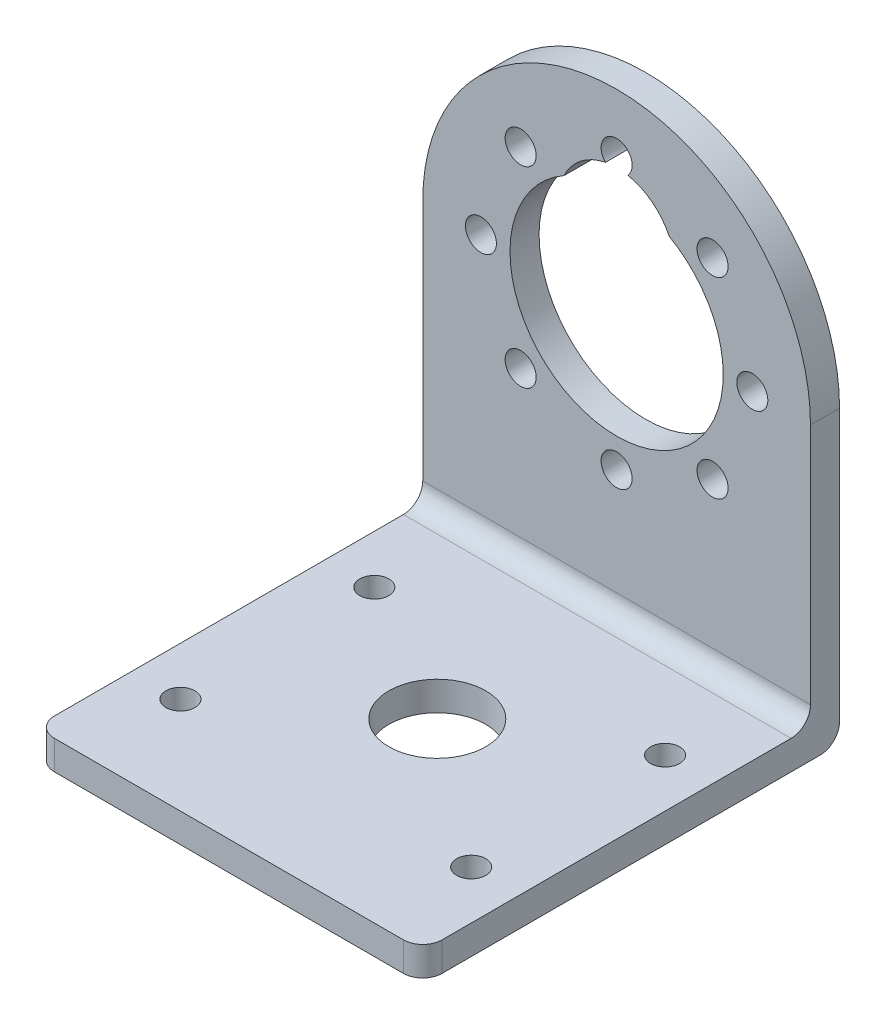
SolidWorks part; units mm, degrees
ref_plane "Front Plane" through (0, 0, 0) normal (0, 0, 1) x (1, 0, 0)
ref_plane "Top Plane" through (0, 0, 0) normal (0, 1, 0) x (1, 0, 0)
ref_plane "Right Plane" through (0, 0, 0) normal (1, 0, 0) x (0, 0, -1)
sketch "Sketch1" plane through (0, 0, 0) normal (0, 1, 0) x (1, 0, 0)
  line L1 (-20, 21.5) -> (20, 21.5)
  line L2 (-20, 21.5) -> (-20, -21.5)
  line L3 (-20, -21.5) -> (20, -21.5)
  line L4 (20, 21.5) -> (20, -21.5)
  line L5 (-20, 21.5) -> (20, -21.5) construction
  line L6 (-20, -21.5) -> (20, 21.5) construction
  circle A0 centre (-15, -11.5) radius 1.5
  circle A1 centre (15, -11.5) radius 1.5
  circle A2 centre (-15, 8.5) radius 1.5
  circle A3 centre (15, 8.5) radius 1.5
  circle A4 centre (0, 0) radius 5
  point P0 (0, 0)
  dimension "D3" = 3
  dimension "D4" = 3
  dimension "D5" = 15
  dimension "D6" = 30
  dimension "D7" = 3
  dimension "D8" = 3
  dimension "D9" = 20
  dimension "D10" = 20
  dimension "D11" = 13
  dimension "D12" = 15
  dimension "D13" = 30
  dimension "D14" = 13
  dimension "D15" = 10
  dimension "D2" = 10
  dimension "D1" = 40
extrude "Boss-Extrude1" add sketch "Sketch1" along normal blind 3
sketch "Sketch3" plane through (0, 0, -21.5) normal (0, 0, -1) x (-1, 0, 0)
  line L1 (-20, 3) -> (20, 3)
  line L2 (-20, 3) -> (-20, 30)
  line L4 (20, 3) -> (20, 30)
  arc A0 (20, 30) -> (-20, 30) centre (0, 30) ccw
  arc A1 (-5.421, 39.5714) -> (5.421, 39.5714) centre (0, 30) ccw
  circle A2 centre (0, 16) radius 1.6
  circle A3 centre (-9.8995, 20.1005) radius 1.6
  circle A4 centre (-14, 30) radius 1.6
  circle A5 centre (-9.8995, 39.8995) radius 1.6
  arc A6 (1.151, 42.8886) -> (-1.151, 42.8886) centre (0, 44) ccw
  circle A7 centre (9.8995, 39.8995) radius 1.6
  circle A8 centre (14, 30) radius 1.6
  circle A9 centre (9.8995, 20.1005) radius 1.6
  arc A10 (5.421, 39.5714) -> (1.151, 42.8886) centre (0, 37) ccw
  arc A11 (-1.151, 42.8886) -> (-5.421, 39.5714) centre (0, 37) ccw
  dimension "D3" = 40
  dimension "D4" = 27
  dimension "D5" = 22
  dimension "D6" = 3.2
  dimension "D7" = 14
  dimension "D8" = 20
  dimension "D10" = 10.1005
  dimension "D11" = 17.1005
  dimension "D12" = 7
  dimension "D13" = 20
  dimension "D14" = 12
  dimension "D1" = 27
  dimension "D2" = 27
  dimension "D9" = 8
extrude "Boss-Extrude2" add sketch "Sketch3" against normal blind 3
fillet "Fillet1" radius 2 4 edges at (20, 1.5, 21.5) (-20, 1.5, 21.5) (0, 0, -21.5) (0, 3, -18.5)
